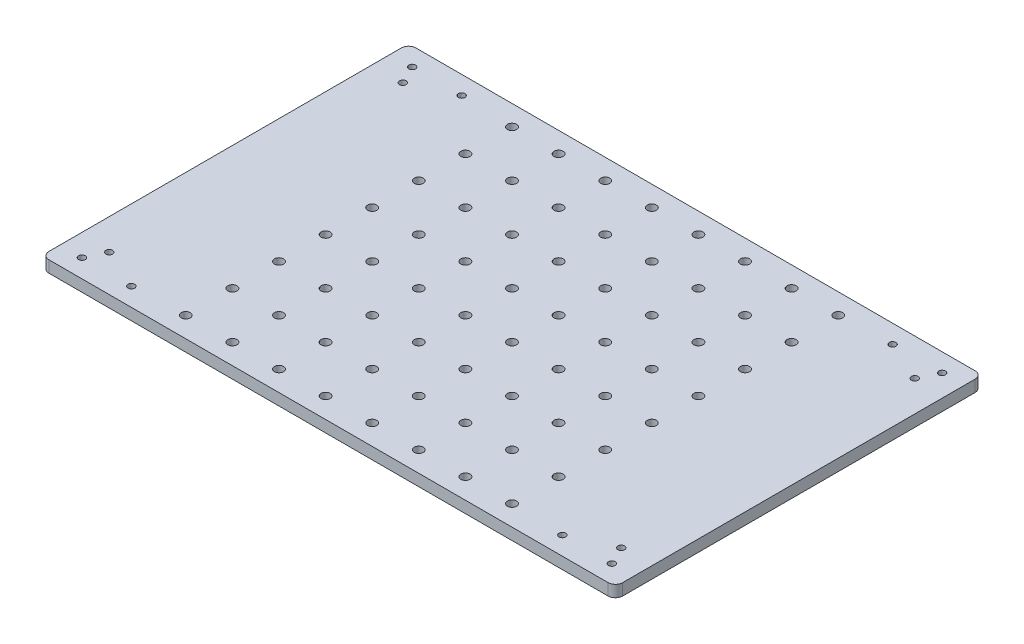
SolidWorks part; units mm, degrees
ref_plane "Front Plane" through (0, 0, 0) normal (0, 0, 1) x (1, 0, 0)
ref_plane "Top Plane" through (0, 0, 0) normal (0, 1, 0) x (1, 0, 0)
ref_plane "Right Plane" through (0, 0, 0) normal (1, 0, 0) x (0, 0, -1)
sketch "Sketch1" plane through (0, 0, 0) normal (0, 1, 0) x (1, 0, 0)
  line L1 (-156.35, -100) -> (156.35, -100)
  line L2 (-156.35, -100) -> (-156.35, 100)
  line L3 (-156.35, 100) -> (156.35, 100)
  line L4 (156.35, -100) -> (156.35, 100)
  line L5 (-156.35, -100) -> (156.35, 100) construction
  line L6 (-156.35, 100) -> (156.35, -100) construction
  point P0 (0, 0)
  dimension "D1" = 312.7
  dimension "D2" = 200
extrude "Boss-Extrude1" add sketch "Sketch1" along normal blind 6.35
fillet "Fillet1" radius 4 4 edges at (-156.35, 3.175, -100) (156.35, 3.175, -100) (156.35, 3.175, 100) (-156.35, 3.175, 100)
sketch "Sketch2" plane through (0, 6.35, 0) normal (0, 1, 0) x (1, 0, 0)
  line L0 (-144.412, 90) -> (-117.4626, 90) construction
  line L2 (-156.35, 96) -> (-156.35, -96) construction
  point P5 (-139.5352, 80)
  dimension "D1" = 26.9494
  dimension "D2" = 90
  dimension "D3" = 11.938
  dimension "D4" = 16.8148
  dimension "D5" = 10
hole_wizard "#6 Clearance Hole1" positions "Sketch3" profile "Sketch4" hole size "#6" standard "ANSI Inch"
sketch "Sketch3" plane through (0, 6.35, 0) normal (0, 1, 0) x (1, 0, 0)
  point P0 (-144.412, 90)
  point P3 (-117.4626, 90)
  point P6 (-139.5352, 80)
sketch "Sketch4" plane through (-144.412, 6.35, -90) normal (1, 0, 0) x (0, 0, 1)
  line L0 (0, 0) -> (0, 7.4489)
  line L1 (0, 7.4489) -> (1.8288, 6.35)
  line L2 (1.8288, 6.35) -> (1.8288, 0)
  line L5 (1.8288, 0) -> (0, 0)
  line L10 (0, 7.4489) -> (-1.8288, 6.35) construction
  line L11 (0, -6.35) -> (0, 107.95) construction
  dimension "Hole Dia." = 3.6576
  dimension "Hole Depth" = 6.35
  dimension "Drill Angle" = 118
mirror "Mirror1" about plane through (0, 0, 0) normal (0, 0, 1) of "#6 Clearance Hole1"
mirror "Mirror2" about plane through (0, 0, 0) normal (1, 0, 0) of "Mirror1", "#6 Clearance Hole1"
sketch "Sketch5" plane through (0, 6.35, 0) normal (0, 1, 0) x (1, 0, 0)
  line L1 (88.9, -88.9) -> (-88.9, -88.9) construction
  line L2 (88.9, -88.9) -> (88.9, 88.9) construction
  line L3 (88.9, 88.9) -> (-88.9, 88.9) construction
  line L4 (-88.9, -88.9) -> (-88.9, 88.9) construction
  line L5 (88.9, -88.9) -> (-88.9, 88.9) construction
  line L6 (88.9, 88.9) -> (-88.9, -88.9) construction
  point P0 (0, 0)
  dimension "D2" = 177.8
hole_wizard "#10 Clearance Hole3" positions "3DSketch5" profile "Sketch9" hole size "#10" standard "ANSI Inch"
sketch3d "3DSketch5"
  point P0 (-88.9, 6.35, 88.9)
sketch "Sketch9" plane through (-88.9, 6.35, 88.9) normal (1, 0, 0) x (0, 0, 1)
  line L0 (0, 0) -> (0, 7.8457)
  line L1 (0, 7.8457) -> (2.4892, 6.35)
  line L2 (2.4892, 6.35) -> (2.4892, 0)
  line L5 (2.4892, 0) -> (0, 0)
  line L10 (0, 7.8457) -> (-2.4892, 6.35) construction
  line L11 (0, -6.35) -> (0, 107.95) construction
  dimension "Hole Dia." = 4.9784
  dimension "Hole Depth" = 6.35
  dimension "Drill Angle" = 118
pattern_linear "LPattern2" count 8 spacing 25.4 along (0, 0, -1) of "#10 Clearance Hole3"
pattern_linear "LPattern3" count 8 spacing 25.4 along (1, 0, 0) of "LPattern2", "#10 Clearance Hole3"
